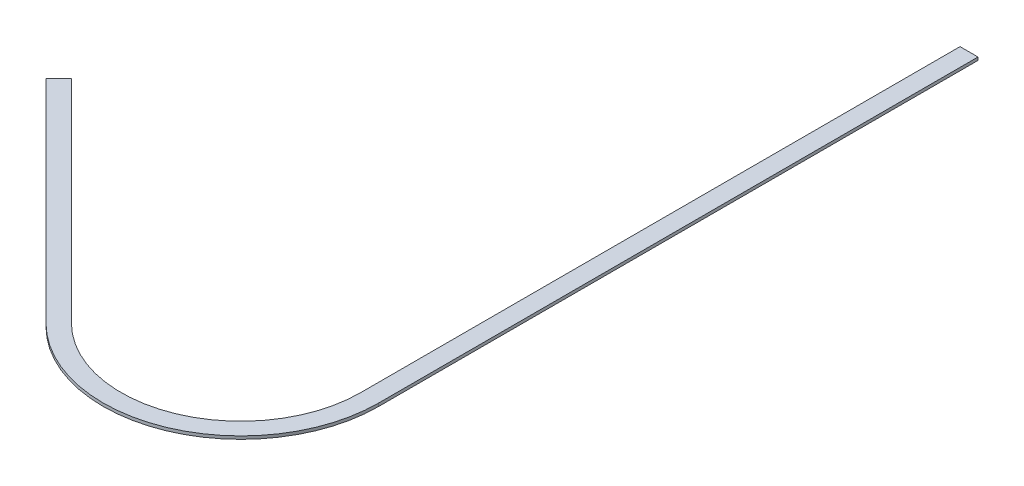
SolidWorks part; units mm, degrees
ref_plane "Front Plane" through (0, 0, 0) normal (0, 0, 1) x (1, 0, 0)
ref_plane "Top Plane" through (0, 0, 0) normal (0, 1, 0) x (1, 0, 0)
ref_plane "Right Plane" through (0, 0, 0) normal (1, 0, 0) x (0, 0, -1)
sketch "Sketch1" plane through (0, 0, 0) normal (0, 1, 0) x (1, 0, 0)
  line L0 (0, 600) -> (0, -400)
  line L4 (30, -400) -> (30, 600)
  line L5 (30, 600) -> (0, 600)
  line L8 (-341.4214, -541.4214) -> (-694.9747, -187.868)
  line L9 (-694.9747, -187.868) -> (-716.188, -209.0812)
  line L10 (-716.188, -209.0812) -> (-362.6346, -562.6346)
  arc A3 (0, -400) -> (-341.4214, -541.4214) centre (-200, -400) cw
  arc A4 (30, -400) -> (-362.6346, -562.6346) centre (-200, -400) cw
  dimension "D2" = 1000
  dimension "D3" = 200
  dimension "D5" = 230
  dimension "D1" = 30
  dimension "D4" = 600
  dimension "D6" = 135
  dimension "D7" = 135
  dimension "D8" = 1000
  dimension "D9" = 500
extrude "Boss-Extrude1" add sketch "Sketch1" along normal blind 5
